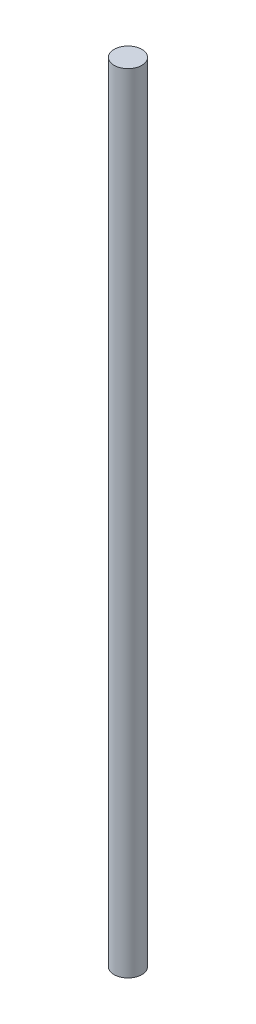
SolidWorks part; units mm, degrees
ref_plane "Alzado" through (0, 0, 0) normal (0, 0, 1) x (1, 0, 0)
ref_plane "Planta" through (0, 0, 0) normal (0, 1, 0) x (1, 0, 0)
ref_plane "Vista lateral" through (0, 0, 0) normal (1, 0, 0) x (0, 0, -1)
sketch "Croquis1" plane through (0, 0, 0) normal (0, 1, 0) x (1, 0, 0)
  circle A0 centre (0, 0) radius 2.5
  dimension "D1" = 5
extrude "Saliente-Extruir1" add sketch "Croquis1" along normal blind 142
